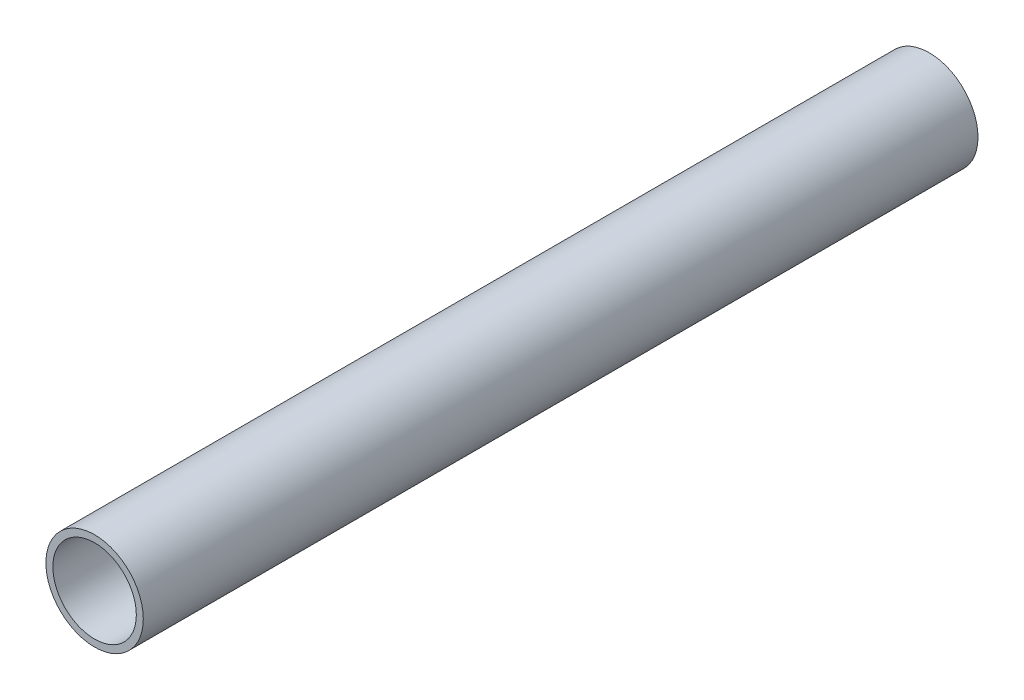
SolidWorks part; units mm, degrees
material "Thornel VCB-20 Carbon Cloth"
ref_plane "Front Plane" through (0, 0, 0) normal (0, 0, 1) x (1, 0, 0)
ref_plane "Top Plane" through (0, 0, 0) normal (0, 1, 0) x (1, 0, 0)
ref_plane "Right Plane" through (0, 0, 0) normal (1, 0, 0) x (0, 0, -1)
sketch "Sketch1" plane through (0, 0, 0) normal (0, 0, 1) x (1, 0, 0)
  circle A0 centre (0, 0) radius 9.525
  circle A1 centre (0, 0) radius 11.1125
  dimension "D1" = 19.05
  dimension "D2" = 22.225
extrude "Boss-Extrude1" add sketch "Sketch1" along normal mid plane 190.5
